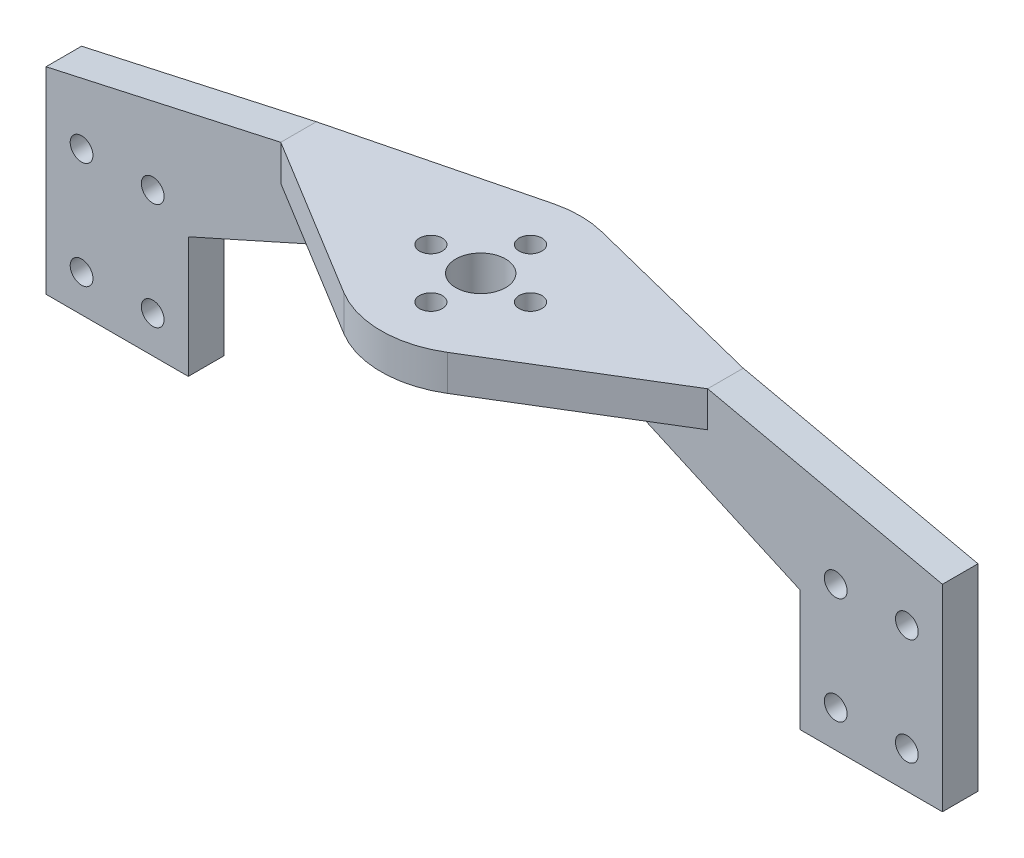
SolidWorks part; units mm, degrees
ref_plane "前视基准面" through (0, 0, 0) normal (0, 0, 1) x (1, 0, 0)
ref_plane "上视基准面" through (0, 0, 0) normal (0, 1, 0) x (1, 0, 0)
ref_plane "右视基准面" through (0, 0, 0) normal (1, 0, 0) x (0, 0, -1)
sketch "草图1" plane through (0, 0, 0) normal (0, 1, 0) x (1, 0, 0)
  line L0 (0, 24.0233) -> (0, 8.1682) construction
  line L1 (-13.2744, 17.0233) -> (29.2277, 17.0233) construction
  line L2 (30, 23.9233) -> (36.7916, 23.9233)
  line L3 (30, 23.9233) -> (3.4103, 30.6015)
  line L4 (30, 18.9233) -> (45, 18.9233)
  line L5 (30, 18.9233) -> (7.2903, 5.0712)
  line L6 (45, 18.9233) -> (45, 23.9233)
  line L7 (45, 23.9233) -> (36.7916, 23.9233)
  line L8 (30, 23.9233) -> (-41.5456, 23.9233) construction
  line L9 (0, 8.1682) -> (0, -4.2952) construction
  line L13 (0, 17.0233) -> (0, 40.7507) construction
  line L14 (-30, 18.9233) -> (-7.2903, 5.0712)
  line L15 (-30, 18.9233) -> (-45, 18.9233)
  line L16 (-45, 18.9233) -> (-45, 23.9233)
  line L17 (-45, 23.9233) -> (-36.7916, 23.9233)
  line L18 (-30, 23.9233) -> (-36.7916, 23.9233)
  line L19 (-30, 23.9233) -> (-3.4103, 30.6015)
  circle A0 centre (0, 24.0233) radius 1.6
  circle A1 centre (0, 10.0233) radius 1.6
  circle A2 centre (-7, 17.0233) radius 1.6
  circle A3 centre (7, 17.0233) radius 1.6
  arc A4 (3.4103, 30.6015) -> (-3.4103, 30.6015) centre (0, 17.0233) ccw
  arc A5 (-7.2903, 5.0712) -> (7.2903, 5.0712) centre (0, 17.0233) ccw
  circle A6 centre (0, 17.0233) radius 3.5
  point P12 (0, 17.0233)
  dimension "D1" = 3.2
  dimension "D2" = 14
  dimension "D4" = 7
  dimension "D5" = 6.9
  dimension "D9" = 7
  dimension "D3" = 7
  dimension "D6" = 30
  dimension "D7" = 5
  dimension "D8" = 15
extrude "凸台-拉伸1" add sketch "草图1" along normal blind 5
sketch "草图3" plane through (0, 0, -23.9233) normal (0, 0, -1) x (-1, 0, 0)
  line L1 (-45, 5) -> (-63, 5)
  line L2 (-63, 5) -> (-63, -30)
  line L3 (-63, -30) -> (-43, -30)
  line L5 (-43, -7.6323) -> (-43, -20.4467)
  line L9 (-45, 0) -> (-30, 0) construction
  line L10 (-53, -30) -> (-53, -2.527) construction
  line L11 (-45, 5) -> (-45, 0) construction
  line L12 (-43, -7.6323) -> (-43, 5)
  line L13 (0, 5) -> (0, -12.6871) construction
  line L17 (-45, 5) -> (-30, 5) construction
  line L18 (-43, 5) -> (-45, 5)
  line L19 (-43, -20.4467) -> (-43, -30)
  line L20 (3.4103, 5) -> (-3.4103, 5) construction
  line L21 (53, -30) -> (53, -2.527) construction
  line L22 (43, -20.4467) -> (43, -30)
  line L23 (43, 5) -> (45, 5)
  line L24 (43, -7.6323) -> (43, 5)
  line L25 (43, -7.6323) -> (43, -20.4467)
  line L26 (63, -30) -> (43, -30)
  line L27 (63, 5) -> (63, -30)
  line L28 (45, 5) -> (63, 5)
  circle A0 centre (-58, -9.8) radius 1.6
  circle A1 centre (-58, -24.8) radius 1.6
  circle A2 centre (-48, -24.8) radius 1.6
  circle A3 centre (-48, -9.8) radius 1.6
  circle A12 centre (48, -9.8) radius 1.6
  circle A13 centre (48, -24.8) radius 1.6
  circle A14 centre (58, -24.8) radius 1.6
  circle A15 centre (58, -9.8) radius 1.6
  dimension "D4" = 9.8
  dimension "D5" = 15
  dimension "D1" = 2
  dimension "D2" = 35
  dimension "D3" = 10
  dimension "D6" = 5
  dimension "D7" = 10
extrude "凸台-拉伸3" add sketch "草图3" against normal blind 5
sketch "草图4" plane through (0, 0, -23.9233) normal (0, 0, -1) x (-1, 0, 0)
  line L0 (-48, -9.8) -> (-48, -24.8) construction
  line L1 (-48, -17.3) -> (-51.5158, -17.3) construction
sketch "草图5" plane through (0, 0, -23.9233) normal (0, 0, -1) x (-1, 0, 0)
  line L0 (14, 0) -> (43, -13)
  line L1 (30, 0) -> (43, 0) construction
  line L2 (43, 0) -> (43, -30) construction
  line L3 (43, -13) -> (43, 0)
  line L4 (43, 0) -> (14, 0)
  line L6 (-43, 0) -> (-30, 0) construction
  line L7 (-43, -30) -> (-43, 0) construction
  line L9 (-43, 0) -> (-14, 0)
  line L10 (-43, 0) -> (-43, -13)
  line L11 (-43, -13) -> (-14, 0)
  dimension "D1" = 13
  dimension "D2" = 29
  dimension "D3" = 29
  dimension "D4" = 13
extrude "凸台-拉伸4" add sketch "草图5" against normal blind 5
sketch "草图6" plane through (0, 0, -23.9233) normal (0, 0, -1) x (-1, 0, 0)
  line L0 (-63, -2.3) -> (-30, 5)
  line L1 (-63, 5) -> (-63, -30) construction
  line L2 (-42.4473, -2.3) -> (-114.75, -2.3) construction
  line L3 (-30, 5) -> (-63, 5)
  line L4 (-63, 5) -> (-63, -2.3)
  line L5 (63, -2.3) -> (30, 5)
  line L6 (63, -30) -> (63, 5) construction
  line L7 (112.7473, -2.3) -> (42.4473, -2.3) construction
  line L8 (30, 5) -> (63, 5)
  line L9 (63, 5) -> (63, -2.3)
extrude "切除-拉伸1" cut sketch "草图6" against normal through all
